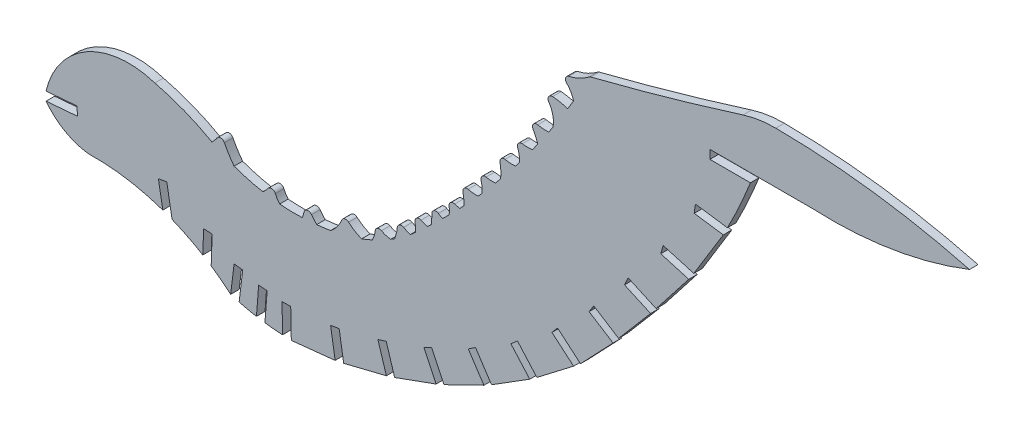
SolidWorks part; units mm, degrees
ref_plane "Front Plane" through (0, 0, 0) normal (0, 0, 1) x (1, 0, 0)
ref_plane "Top Plane" through (0, 0, 0) normal (0, 1, 0) x (1, 0, 0)
ref_plane "Right Plane" through (0, 0, 0) normal (1, 0, 0) x (0, 0, -1)
sketch "Sketch1" plane through (0, 0, 0) normal (0, 0, 1) x (1, 0, 0)
  line L0 (42.0206, 28.9091) -> (42.0206, 30.4621)
  line L1 (42.0206, 28.9091) -> (49.265, 28.9084)
  line L2 (39.4362, 20.7034) -> (45.1534, 19.8921)
  line L3 (39.2188, 19.1656) -> (39.4362, 20.7034)
  line L4 (39.2188, 19.1656) -> (44.416, 18.428)
  line L5 (39.1492, 9.8342) -> (44.416, 18.428)
  line L6 (33.6753, 11.4198) -> (39.1492, 9.8342)
  line L7 (33.2465, 9.9268) -> (33.6753, 11.4198)
  line L9 (33.2465, 9.9268) -> (38.2491, 8.4779)
  line L10 (32.4299, 1.0301) -> (38.2491, 8.4779)
  line L11 (27.4088, 3.29) -> (32.4299, 1.0301)
  line L12 (-54.023, -28.4091) -> (-54.9652, -23.0657)
  line L13 (26.7692, 1.8744) -> (27.4088, 3.29)
  line L14 (26.7692, 1.8744) -> (31.432, -0.2238)
  line L15 (25.7202, -6.9259) -> (31.432, -0.2238)
  line L16 (21.2758, -4.116) -> (25.7202, -6.9259)
  line L17 (-55.68, -27.7885) -> (-56.4661, -23.3304)
  line L18 (20.4439, -5.4277) -> (21.2758, -4.116)
  line L19 (20.4439, -5.4277) -> (24.7307, -8.138)
  line L20 (18.9109, -14.2545) -> (24.7307, -8.138)
  line L21 (14.8196, -10.7737) -> (18.9109, -14.2545)
  line L22 (13.8131, -11.9567) -> (14.8196, -10.7737)
  line L23 (13.8131, -11.9567) -> (17.6788, -15.2454)
  line L24 (11.1241, -20.27) -> (17.6788, -15.2454)
  line L25 (7.6548, -16.3531) -> (11.1241, -20.27)
  line L26 (6.4925, -17.3837) -> (7.6548, -16.3531)
  line L27 (6.4925, -17.3837) -> (9.8521, -21.1758)
  line L28 (3.0249, -25.4479) -> (9.8521, -21.1758)
  line L29 (0.1669, -21.1227) -> (3.0249, -25.4479)
  line L30 (-1.1299, -21.9783) -> (0.1669, -21.1227)
  line L31 (-47.0412, -32.1069) -> (-46.869, -27.0782)
  line L32 (-1.1299, -21.9783) -> (1.6647, -26.2063)
  line L33 (-5.4605, -29.6805) -> (1.6647, -26.2063)
  line L34 (-7.6594, -25.0457) -> (-5.4605, -29.6805)
  line L35 (-9.0625, -25.7113) -> (-7.6594, -25.0457)
  line L36 (-9.0625, -25.7113) -> (-6.8873, -30.2959)
  line L37 (-14.2768, -32.9758) -> (-6.8873, -30.2959)
  line L38 (-15.7857, -28.1319) -> (-14.2768, -32.9758)
  line L39 (-17.2686, -28.5936) -> (-15.7857, -28.1319)
  line L40 (-54.9652, -23.0657) -> (-56.4661, -23.3304)
  line L41 (-17.2686, -28.5936) -> (-15.7545, -33.4511)
  line L42 (-23.3788, -35.3326) -> (-15.7545, -33.4511)
  line L43 (-24.1844, -30.3731) -> (-23.3788, -35.3326)
  line L44 (-25.7166, -30.6229) -> (-24.1844, -30.3731)
  line L45 (-48.5335, -31.1531) -> (-48.3921, -27.026)
  line L46 (-25.7166, -30.6229) -> (-24.9013, -35.6463)
  line L47 (-32.7325, -36.4694) -> (-24.9013, -35.6463)
  line L48 (-32.8383, -31.2607) -> (-32.7325, -36.4694)
  line L49 (-37.4432, -36.0988) -> (-37.0479, -30.9542)
  line L50 (-34.3902, -31.2919) -> (-32.8383, -31.2607)
  line L51 (-34.3902, -31.2919) -> (-34.2878, -36.3792)
  line L52 (-42.0468, -35.1884) -> (-41.4058, -29.9128)
  line L53 (-42.9487, -29.7254) -> (-41.4058, -29.9128)
  line L54 (-46.869, -27.0782) -> (-48.3921, -27.026)
  line L55 (-43.5584, -34.7571) -> (-42.9487, -29.7254)
  line L56 (-38.9538, -35.8669) -> (-38.5675, -30.8374)
  line L58 (-76.5243, -21.3591) -> (-70.9023, -20.8906)
  line L59 (-71.0257, -19.3486) -> (-70.9023, -20.8906)
  line L60 (-76.5383, -19.8126) -> (-71.0257, -19.3486)
  line L61 (-37.0479, -30.9542) -> (-38.5675, -30.8374)
  line L63 (42.0206, 30.4621) -> (60.2091, 30.4621)
  arc A0 (-68.9979, -25.7113) -> (-55.68, -27.7885) centre (-68.0431, -63.3208) cw
  arc A1 (-68.9979, -25.7113) -> (-76.5243, -21.3591) centre (-67.616, -14.6376) cw
  arc A2 (-76.5383, -19.8126) -> (-57.1032, -8.8383) centre (-61.7748, -23.2616) cw
  arc A3 (45.1534, 19.8921) -> (49.265, 28.9084) centre (-42.7103, 65.4042) ccw
  arc A4 (-57.1032, -8.8383) -> (-46.8999, -12.8696) centre (-66.4801, -47.4997) cw
  arc A5 (-42.9487, -14.6218) -> (-37.8077, -16.0147) centre (-32.1428, 15.0765) ccw
  arc A6 (20.4769, 30.8752) -> (16.8258, 29.1543) centre (14.67, 38.4615) cw
  arc A7 (16.4635, 27.8686) -> (17.6788, 25.7931) centre (13.2333, 24.5837) cw
  arc A8 (13.9998, 19.8921) -> (13.2513, 23.3895) centre (9.4467, 20.7464) ccw
  arc A9 (13.9388, 24.5837) -> (16.6279, 24.0427) centre (12.9908, 12.9187) cw
  arc A10 (13.2333, 18.7373) -> (11.281, 18.89) centre (12.7572, 25.2035) cw
  arc A11 (10.4385, 17.7832) -> (11.2927, 15.9149) centre (-2.3776, 10.7946) cw
  arc A12 (10.3223, 14.555) -> (8.5235, 14.5727) centre (9.4897, 21.3186) cw
  arc A13 (7.7034, 13.5471) -> (7.9939, 11.4198) centre (3.2717, 11.8585) cw
  arc A14 (7.3004, 10.5187) -> (5.4283, 10.6074) centre (6.6543, 16.6856) cw
  arc A15 (4.5326, 9.7002) -> (4.6478, 7.2004) centre (-2.8783, 8.1062) cw
  arc A16 (3.7366, 6.1047) -> (2.047, 6.1857) centre (3.1653, 11.8513) cw
  arc A17 (1.1589, 5.2584) -> (1.311, 3.29) centre (-4.8267, 3.8057) cw
  arc A18 (0.6301, 2.5251) -> (-1.1615, 2.6952) centre (0.2803, 8.3607) cw
  arc A19 (-2.0908, 1.7806) -> (-1.8985, -0.2238) centre (-9.2327, 0.0842) cw
  arc A20 (-2.6291, -0.9924) -> (-3.5629, -0.785) centre (-2.0392, 3.8696) cw
  arc A21 (-4.5539, -1.6201) -> (-4.545, -2.9564) centre (-9.3113, -2.32) cw
  arc A22 (-5.7106, -4.116) -> (-6.468, -3.6889) centre (-3.0102, 1.5582) cw
  arc A23 (-7.6488, -4.3543) -> (-7.7436, -6.0777) centre (-16.919, -4.7084) cw
  arc A24 (-8.3914, -6.6871) -> (-9.5741, -6.2807) centre (-6.928, -0.5047) cw
  arc A25 (-10.647, -7.072) -> (-10.5158, -8.6347) centre (-27.585, -9.2811) cw
  arc A26 (-11.4836, -9.4677) -> (-12.6722, -8.9396) centre (-9.3263, -3.0108) cw
  arc A27 (-13.8053, -9.5311) -> (-14.2768, -11.5145) centre (-21.1503, -8.8326) cw
  arc A28 (-14.9799, -11.9567) -> (-16.631, -11.4494) centre (-14.5487, -7.6126) cw
  arc A29 (-17.7507, -12.0257) -> (-18.2706, -13.6961) centre (-22.6338, -11.4219) cw
  arc A30 (-20.1769, -14.4812) -> (-22.514, -13.0689) centre (-17.5761, -7.5375) cw
  arc A31 (-23.728, -13.352) -> (-25.7166, -15.9657) centre (-29.5077, -11.0177) cw
  arc A32 (-28.1905, -16.2785) -> (-29.1249, -15.2071) centre (-20.896, -8.9728) cw
  arc A33 (-30.478, -15.5106) -> (-30.7493, -16.4959) centre (-38.6032, -13.8036) cw
  arc A34 (-34.812, -16.4137) -> (-35.5792, -15.1853) centre (-31.1109, -13.2484) cw
  arc A35 (-36.8913, -15.0357) -> (-37.8077, -16.0147) centre (-41.5392, -11.6037) cw
  arc A36 (-42.9487, -14.6218) -> (-44.6789, -11.8668) centre (-29.0257, -3.9566) cw
  arc A37 (-45.9891, -11.7819) -> (-46.8999, -12.8696) centre (-51.8738, -7.7788) cw
  arc A38 (-34.812, -16.4137) -> (-30.7493, -16.4959) centre (-32.1428, 15.0765) ccw
  arc A39 (-20.1769, -14.4812) -> (-18.2706, -13.6961) centre (-30.7493, 13.8947) ccw
  arc A40 (-14.9799, -11.9567) -> (-14.2768, -11.5145) centre (-30.7493, 13.8947) ccw
  arc A41 (-11.4836, -9.4677) -> (-10.5158, -8.6347) centre (-30.7493, 13.8947) ccw
  arc A42 (-5.7106, -4.116) -> (-4.545, -2.9564) centre (-108.4736, 100.3467) ccw
  arc A43 (-2.6291, -0.9924) -> (-1.8985, -0.2238) centre (-108.4736, 100.3467) ccw
  arc A44 (0.6301, 2.5251) -> (1.311, 3.29) centre (-108.4736, 100.3467) ccw
  arc A45 (3.7366, 6.1047) -> (4.6478, 7.2004) centre (-108.4736, 100.3467) ccw
  arc A46 (7.3004, 10.5187) -> (7.9939, 11.4198) centre (-108.4736, 100.3467) ccw
  arc A47 (10.3223, 14.555) -> (11.2927, 15.9149) centre (-108.4736, 100.3467) ccw
  arc A48 (13.2333, 18.7373) -> (13.9998, 19.8921) centre (-108.4736, 100.3467) ccw
  arc A49 (16.6279, 24.0427) -> (17.6788, 25.7931) centre (-108.4736, 100.3467) ccw
  arc A50 (-42.0468, -35.1884) -> (-38.9538, -35.8669) centre (-32.6035, 0.4702) ccw
  arc A51 (-44.6789, -11.8668) -> (-45.9891, -11.7819) centre (-45.359, -12.2105) ccw
  arc A52 (-35.5792, -15.1853) -> (-36.8913, -15.0357) centre (-36.2783, -15.4883) ccw
  arc A53 (-29.1249, -15.2071) -> (-30.478, -15.5106) centre (-29.7323, -15.6673) ccw
  arc A54 (-22.514, -13.0689) -> (-23.728, -13.352) centre (-23.0214, -13.6374) ccw
  arc A55 (-16.631, -11.4494) -> (-17.7507, -12.0257) centre (-16.9945, -12.1192) ccw
  arc A56 (-12.6722, -8.9396) -> (-13.8053, -9.5311) centre (-13.0467, -9.6033) ccw
  arc A57 (-9.5741, -6.2807) -> (-10.647, -7.072) centre (-9.8914, -6.9734) ccw
  arc A58 (-6.468, -3.6889) -> (-7.6488, -4.3543) centre (-6.8873, -4.3252) ccw
  arc A59 (-3.5629, -0.785) -> (-4.5539, -1.6201) centre (-3.8, -1.5092) ccw
  arc A60 (-1.1615, 2.6952) -> (-2.0908, 1.7806) centre (-1.3494, 1.9567) ccw
  arc A61 (2.047, 6.1857) -> (1.1589, 5.2584) centre (1.8994, 5.4381) ccw
  arc A62 (5.4283, 10.6074) -> (4.5326, 9.7002) centre (5.2776, 9.8605) ccw
  arc A63 (8.5235, 14.5727) -> (7.7034, 13.5471) centre (8.4155, 13.8184) ccw
  arc A64 (11.281, 18.89) -> (10.4385, 17.7832) centre (11.1075, 18.148) ccw
  arc A65 (13.2513, 23.3895) -> (13.9388, 24.5837) centre (13.8771, 23.8242) cw
  arc A66 (-28.1905, -16.2785) -> (-25.7166, -15.9657) centre (-30.7493, 13.8947) ccw
  arc A67 (-8.3914, -6.6871) -> (-7.7436, -6.0777) centre (-108.4736, 100.3467) ccw
  arc A68 (20.4769, 30.8752) -> (20.7526, 31.0088) centre (20.94, 30.2702) cw
  arc A69 (47.9456, 38.74) -> (53.7989, 39.6218) centre (53.6757, 20.5722) cw
  arc A70 (16.8258, 29.1543) -> (16.4635, 27.8686) centre (16.9978, 28.412) ccw
  arc A71 (20.7526, 31.0088) -> (47.9456, 38.74) centre (-101.1249, 511.3764) ccw
  arc A72 (53.7989, 39.6218) -> (88.3762, 35.0509) centre (52.8941, -100.2923) cw
  arc A73 (88.3762, 35.0509) -> (60.2091, 30.4621) centre (63.607, 98.3466) cw
  arc A74 (-54.023, -28.4091) -> (-48.5335, -31.1531) centre (-68.0431, -63.3208) cw
  arc A75 (-47.0412, -32.1069) -> (-43.5584, -34.7571) centre (-68.0431, -63.3208) cw
  arc A76 (-37.4432, -36.0988) -> (-34.2878, -36.3792) centre (-32.6035, 0.4702) ccw
  point P200 (-38.9589, -35.9324)
  dimension "D1" = 0.762
  dimension "D2" = 19.05
extrude "Boss-Extrude1" add sketch "Sketch1" along normal blind 1.524
